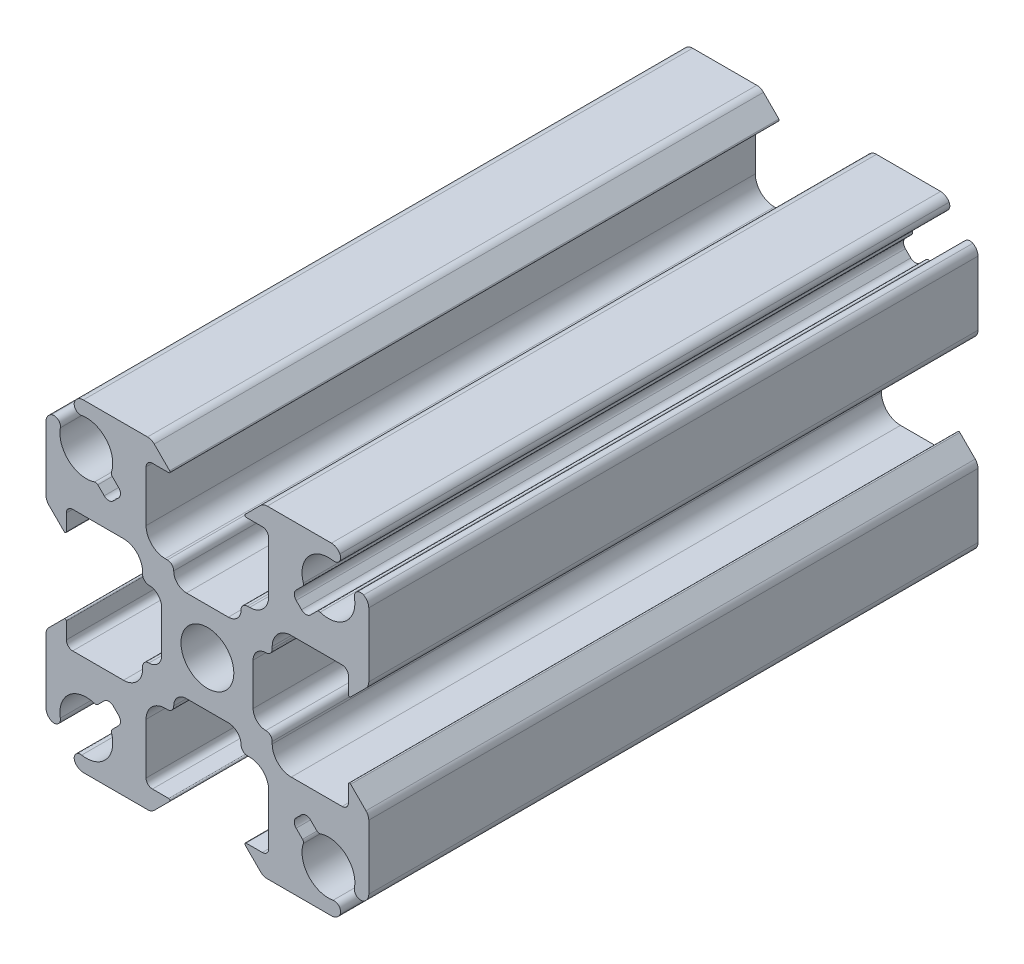
SolidWorks part; units mm, degrees
ref_plane "Front Plane" through (0, 0, 0) normal (0, 0, 1) x (1, 0, 0)
ref_plane "Top Plane" through (0, 0, 0) normal (0, 1, 0) x (1, 0, 0)
ref_plane "Right Plane" through (0, 0, 0) normal (1, 0, 0) x (0, 0, -1)
ref_plane "Plane1" through (0, 0, 0) normal (0, 0, -1) x (-1, 0, 0)
sketch "Sketch1" plane through (0, 0, 0) normal (0, 0, -1) x (-1, 0, 0)
  line L0 (-7.4885, 8.6199) -> (-6.9856, 8.117)
  line L1 (-6.9856, 7.4099) -> (-7.4099, 6.9856)
  line L2 (-8.117, 6.9856) -> (-8.6199, 7.4885)
  line L3 (-12.7, 9.7594) -> (-12.7, 4.7107)
  line L4 (-12.4803, 4.1803) -> (-11.2707, 2.9707)
  line L5 (-11.1, 3.0414) -> (-11.1, 4.325)
  line L6 (-10.6, 4.825) -> (-6.6, 4.825)
  line L7 (-5.1, 3.325) -> (-5.1, 3.15)
  line L8 (-3.6, 1.65) -> (-3.6, -1.65)
  line L9 (-5.1, -3.15) -> (-5.1, -3.325)
  line L10 (-6.6, -4.825) -> (-10.6, -4.825)
  line L11 (-11.1, -4.325) -> (-11.1, -3.0414)
  line L12 (-11.2707, -2.9707) -> (-12.4803, -4.1803)
  line L13 (-12.7, -4.7107) -> (-12.7, -9.7594)
  line L14 (-8.6199, -7.4885) -> (-8.117, -6.9856)
  line L15 (-7.4099, -6.9856) -> (-6.9856, -7.4099)
  line L16 (-6.9856, -8.117) -> (-7.4885, -8.6199)
  line L17 (-9.7594, -12.7) -> (-4.7107, -12.7)
  line L18 (-4.1803, -12.4803) -> (-2.9707, -11.2707)
  line L19 (-3.0414, -11.1) -> (-4.325, -11.1)
  line L20 (-4.825, -10.6) -> (-4.825, -6.6)
  line L21 (-3.325, -5.1) -> (-3.15, -5.1)
  line L22 (-1.65, -3.6) -> (1.65, -3.6)
  line L23 (3.15, -5.1) -> (3.325, -5.1)
  line L24 (4.825, -6.6) -> (4.825, -10.6)
  line L25 (4.325, -11.1) -> (3.0414, -11.1)
  line L26 (2.9707, -11.2707) -> (4.1803, -12.4803)
  line L27 (4.7107, -12.7) -> (9.7594, -12.7)
  line L28 (7.4885, -8.6199) -> (6.9856, -8.117)
  line L29 (6.9856, -7.4099) -> (7.4099, -6.9856)
  line L30 (8.117, -6.9856) -> (8.6199, -7.4885)
  line L31 (12.7, -9.7594) -> (12.7, -4.7107)
  line L32 (12.4803, -4.1803) -> (11.2707, -2.9707)
  line L33 (11.1, -3.0414) -> (11.1, -4.325)
  line L34 (10.6, -4.825) -> (6.6, -4.825)
  line L35 (5.1, -3.325) -> (5.1, -3.15)
  line L36 (3.6, -1.65) -> (3.6, 1.65)
  line L37 (5.1, 3.15) -> (5.1, 3.325)
  line L38 (6.6, 4.825) -> (10.6, 4.825)
  line L39 (11.1, 4.325) -> (11.1, 3.0414)
  line L40 (11.2707, 2.9707) -> (12.4803, 4.1803)
  line L41 (12.7, 4.7107) -> (12.7, 9.7594)
  line L42 (8.6199, 7.4885) -> (8.117, 6.9856)
  line L43 (7.4099, 6.9856) -> (6.9856, 7.4099)
  line L44 (6.9856, 8.117) -> (7.4885, 8.6199)
  line L45 (9.7594, 12.7) -> (4.7107, 12.7)
  line L46 (4.1803, 12.4803) -> (2.9707, 11.2707)
  line L47 (3.0414, 11.1) -> (4.325, 11.1)
  line L48 (4.825, 10.6) -> (4.825, 6.6)
  line L49 (3.325, 5.1) -> (3.15, 5.1)
  line L50 (1.65, 3.6) -> (-1.65, 3.6)
  line L51 (-3.15, 5.1) -> (-3.325, 5.1)
  line L52 (-4.825, 6.6) -> (-4.825, 10.6)
  line L53 (-4.325, 11.1) -> (-3.0414, 11.1)
  line L54 (-2.9707, 11.2707) -> (-4.1803, 12.4803)
  line L55 (-4.7107, 12.7) -> (-9.7594, 12.7)
  circle A0 centre (0, 0) radius 2.08
  arc A1 (-9.7594, 12.7) -> (-10.4266, 12.2927) centre (-9.7594, 11.95) ccw
  arc A2 (-10.4266, 12.2927) -> (-9.8933, 11.5721) centre (-9.9818, 12.0642) ccw
  arc A3 (-9.8933, 11.5721) -> (-7.5492, 8.8748) centre (-9.525, 9.525) cw
  arc A4 (-7.5492, 8.8748) -> (-7.4885, 8.6199) centre (-7.3118, 8.7967) ccw
  arc A5 (-6.9856, 8.117) -> (-6.9856, 7.4099) centre (-7.3392, 7.7635) cw
  arc A6 (-7.4099, 6.9856) -> (-8.117, 6.9856) centre (-7.7635, 7.3392) cw
  arc A7 (-8.6199, 7.4885) -> (-8.8748, 7.5492) centre (-8.7967, 7.3118) ccw
  arc A8 (-8.8748, 7.5492) -> (-11.5721, 9.8933) centre (-9.525, 9.525) cw
  arc A9 (-11.5721, 9.8933) -> (-12.2927, 10.4266) centre (-12.0642, 9.9818) ccw
  arc A10 (-12.2927, 10.4266) -> (-12.7, 9.7594) centre (-11.95, 9.7594) ccw
  arc A11 (-12.7, 4.7107) -> (-12.4803, 4.1803) centre (-11.95, 4.7107) ccw
  arc A12 (-11.2707, 2.9707) -> (-11.1, 3.0414) centre (-11.2, 3.0414) ccw
  arc A13 (-11.1, 4.325) -> (-10.6, 4.825) centre (-10.6, 4.325) cw
  arc A14 (-6.6, 4.825) -> (-5.1, 3.325) centre (-6.6, 3.325) cw
  arc A15 (-5.1, 3.15) -> (-4.6, 2.65) centre (-4.6, 3.15) ccw
  arc A16 (-4.6, 2.65) -> (-3.6, 1.65) centre (-4.6, 1.65) cw
  arc A17 (-3.6, -1.65) -> (-4.6, -2.65) centre (-4.6, -1.65) cw
  arc A18 (-4.6, -2.65) -> (-5.1, -3.15) centre (-4.6, -3.15) ccw
  arc A19 (-5.1, -3.325) -> (-6.6, -4.825) centre (-6.6, -3.325) cw
  arc A20 (-10.6, -4.825) -> (-11.1, -4.325) centre (-10.6, -4.325) cw
  arc A21 (-11.1, -3.0414) -> (-11.2707, -2.9707) centre (-11.2, -3.0414) ccw
  arc A22 (-12.4803, -4.1803) -> (-12.7, -4.7107) centre (-11.95, -4.7107) ccw
  arc A23 (-12.7, -9.7594) -> (-12.2927, -10.4266) centre (-11.95, -9.7594) ccw
  arc A24 (-12.2927, -10.4266) -> (-11.5721, -9.8933) centre (-12.0642, -9.9818) ccw
  arc A25 (-11.5721, -9.8933) -> (-8.8748, -7.5492) centre (-9.525, -9.525) cw
  arc A26 (-8.8748, -7.5492) -> (-8.6199, -7.4885) centre (-8.7967, -7.3118) ccw
  arc A27 (-8.117, -6.9856) -> (-7.4099, -6.9856) centre (-7.7635, -7.3392) cw
  arc A28 (-6.9856, -7.4099) -> (-6.9856, -8.117) centre (-7.3392, -7.7635) cw
  arc A29 (-7.4885, -8.6199) -> (-7.5492, -8.8748) centre (-7.3118, -8.7967) ccw
  arc A30 (-7.5492, -8.8748) -> (-9.8933, -11.5721) centre (-9.525, -9.525) cw
  arc A31 (-9.8933, -11.5721) -> (-10.4266, -12.2927) centre (-9.9818, -12.0642) ccw
  arc A32 (-10.4266, -12.2927) -> (-9.7594, -12.7) centre (-9.7594, -11.95) ccw
  arc A33 (-4.7107, -12.7) -> (-4.1803, -12.4803) centre (-4.7107, -11.95) ccw
  arc A34 (-2.9707, -11.2707) -> (-3.0414, -11.1) centre (-3.0414, -11.2) ccw
  arc A35 (-4.325, -11.1) -> (-4.825, -10.6) centre (-4.325, -10.6) cw
  arc A36 (-4.825, -6.6) -> (-3.325, -5.1) centre (-3.325, -6.6) cw
  arc A37 (-3.15, -5.1) -> (-2.65, -4.6) centre (-3.15, -4.6) ccw
  arc A38 (-2.65, -4.6) -> (-1.65, -3.6) centre (-1.65, -4.6) cw
  arc A39 (1.65, -3.6) -> (2.65, -4.6) centre (1.65, -4.6) cw
  arc A40 (2.65, -4.6) -> (3.15, -5.1) centre (3.15, -4.6) ccw
  arc A41 (3.325, -5.1) -> (4.825, -6.6) centre (3.325, -6.6) cw
  arc A42 (4.825, -10.6) -> (4.325, -11.1) centre (4.325, -10.6) cw
  arc A43 (3.0414, -11.1) -> (2.9707, -11.2707) centre (3.0414, -11.2) ccw
  arc A44 (4.1803, -12.4803) -> (4.7107, -12.7) centre (4.7107, -11.95) ccw
  arc A45 (9.7594, -12.7) -> (10.4266, -12.2927) centre (9.7594, -11.95) ccw
  arc A46 (10.4266, -12.2927) -> (9.8933, -11.5721) centre (9.9818, -12.0642) ccw
  arc A47 (9.8933, -11.5721) -> (7.5492, -8.8748) centre (9.525, -9.525) cw
  arc A48 (7.5492, -8.8748) -> (7.4885, -8.6199) centre (7.3118, -8.7967) ccw
  arc A49 (6.9856, -8.117) -> (6.9856, -7.4099) centre (7.3392, -7.7635) cw
  arc A50 (7.4099, -6.9856) -> (8.117, -6.9856) centre (7.7635, -7.3392) cw
  arc A51 (8.6199, -7.4885) -> (8.8748, -7.5492) centre (8.7967, -7.3118) ccw
  arc A52 (8.8748, -7.5492) -> (11.5721, -9.8933) centre (9.525, -9.525) cw
  arc A53 (11.5721, -9.8933) -> (12.2927, -10.4266) centre (12.0642, -9.9818) ccw
  arc A54 (12.2927, -10.4266) -> (12.7, -9.7594) centre (11.95, -9.7594) ccw
  arc A55 (12.7, -4.7107) -> (12.4803, -4.1803) centre (11.95, -4.7107) ccw
  arc A56 (11.2707, -2.9707) -> (11.1, -3.0414) centre (11.2, -3.0414) ccw
  arc A57 (11.1, -4.325) -> (10.6, -4.825) centre (10.6, -4.325) cw
  arc A58 (6.6, -4.825) -> (5.1, -3.325) centre (6.6, -3.325) cw
  arc A59 (5.1, -3.15) -> (4.6, -2.65) centre (4.6, -3.15) ccw
  arc A60 (4.6, -2.65) -> (3.6, -1.65) centre (4.6, -1.65) cw
  arc A61 (3.6, 1.65) -> (4.6, 2.65) centre (4.6, 1.65) cw
  arc A62 (4.6, 2.65) -> (5.1, 3.15) centre (4.6, 3.15) ccw
  arc A63 (5.1, 3.325) -> (6.6, 4.825) centre (6.6, 3.325) cw
  arc A64 (10.6, 4.825) -> (11.1, 4.325) centre (10.6, 4.325) cw
  arc A65 (11.1, 3.0414) -> (11.2707, 2.9707) centre (11.2, 3.0414) ccw
  arc A66 (12.4803, 4.1803) -> (12.7, 4.7107) centre (11.95, 4.7107) ccw
  arc A67 (12.7, 9.7594) -> (12.2927, 10.4266) centre (11.95, 9.7594) ccw
  arc A68 (12.2927, 10.4266) -> (11.5721, 9.8933) centre (12.0642, 9.9818) ccw
  arc A69 (11.5721, 9.8933) -> (8.8748, 7.5492) centre (9.525, 9.525) cw
  arc A70 (8.8748, 7.5492) -> (8.6199, 7.4885) centre (8.7967, 7.3118) ccw
  arc A71 (8.117, 6.9856) -> (7.4099, 6.9856) centre (7.7635, 7.3392) cw
  arc A72 (6.9856, 7.4099) -> (6.9856, 8.117) centre (7.3392, 7.7635) cw
  arc A73 (7.4885, 8.6199) -> (7.5492, 8.8748) centre (7.3118, 8.7967) ccw
  arc A74 (7.5492, 8.8748) -> (9.8933, 11.5721) centre (9.525, 9.525) cw
  arc A75 (9.8933, 11.5721) -> (10.4266, 12.2927) centre (9.9818, 12.0642) ccw
  arc A76 (10.4266, 12.2927) -> (9.7594, 12.7) centre (9.7594, 11.95) ccw
  arc A77 (4.7107, 12.7) -> (4.1803, 12.4803) centre (4.7107, 11.95) ccw
  arc A78 (2.9707, 11.2707) -> (3.0414, 11.1) centre (3.0414, 11.2) ccw
  arc A79 (4.325, 11.1) -> (4.825, 10.6) centre (4.325, 10.6) cw
  arc A80 (4.825, 6.6) -> (3.325, 5.1) centre (3.325, 6.6) cw
  arc A81 (3.15, 5.1) -> (2.65, 4.6) centre (3.15, 4.6) ccw
  arc A82 (2.65, 4.6) -> (1.65, 3.6) centre (1.65, 4.6) cw
  arc A83 (-1.65, 3.6) -> (-2.65, 4.6) centre (-1.65, 4.6) cw
  arc A84 (-2.65, 4.6) -> (-3.15, 5.1) centre (-3.15, 4.6) ccw
  arc A85 (-3.325, 5.1) -> (-4.825, 6.6) centre (-3.325, 6.6) cw
  arc A86 (-4.825, 10.6) -> (-4.325, 11.1) centre (-4.325, 10.6) cw
  arc A87 (-3.0414, 11.1) -> (-2.9707, 11.2707) centre (-3.0414, 11.2) ccw
  arc A88 (-4.1803, 12.4803) -> (-4.7107, 12.7) centre (-4.7107, 11.95) ccw
extrude "Boss-Extrude1" add sketch "Sketch1" against normal mid plane 47.9406
